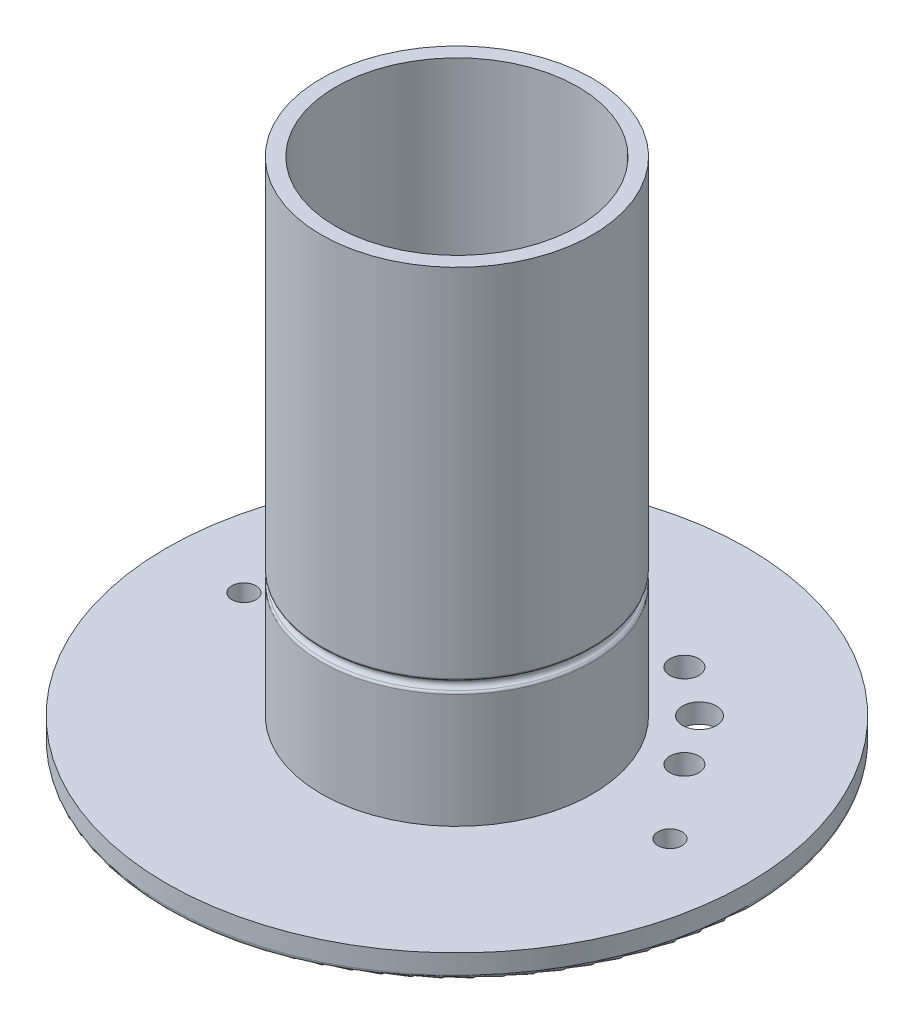
SolidWorks part; units mm, degrees
ref_plane "Front Plane" through (0, 0, 0) normal (0, 0, 1) x (1, 0, 0)
ref_plane "Top Plane" through (0, 0, 0) normal (0, 1, 0) x (1, 0, 0)
ref_plane "Right Plane" through (0, 0, 0) normal (1, 0, 0) x (0, 0, -1)
sketch "Sketch1" plane through (0, 0, 0) normal (0, 1, 0) x (1, 0, 0)
  circle A0 centre (0, 0) radius 60
extrude "Boss-Extrude1" add sketch "Sketch1" along normal blind 5
sketch "Sketch2" plane through (0, 5, 0) normal (0, 1, 0) x (1, 0, 0)
  circle A1 centre (-44, 0) radius 2.5
  circle A2 centre (44, 0) radius 2.5
extrude "Cut-Extrude1" cut sketch "Sketch2" against normal blind 5
sketch "Sketch3" plane through (0, 5, 0) normal (0, 1, 0) x (1, 0, 0)
  circle A0 centre (0, 0) radius 28
extrude "Boss-Extrude2" add sketch "Sketch3" along normal blind 100
sketch "Sketch5" plane through (0, 105, 0) normal (0, 1, 0) x (1, 0, 0)
  circle A0 centre (0, 0) radius 25
extrude "Cut-Extrude3" cut sketch "Sketch5" against normal blind 105
ref_axis "Axis1" through (0, 105, 0) along (0, -1, 0)
sketch "Sketch6" plane through (0, 5, 0) normal (0, 1, 0) x (1, 0, 0)
  line L0 (0, 28) -> (0, 60)
  circle A0 centre (0, 0) radius 28 construction
  circle A1 centre (0, 0) radius 60 construction
ref_plane "Plane1" through (0, 0, 0) normal (1, 0, 0) x (0, 0, -1)
sketch "Sketch7" plane through (0, 0, 0) normal (1, 0, 0) x (0, 0, -1)
  line L2 (28, 5) -> (28, 105) construction
  circle A0 centre (28, 30) radius 1
revolve "Cut-Revolve1" cut sketch "Sketch7" angle 360 about axis through (0, 105, 0) along (0, -1, 0)
fillet "Fillet2" radius 1 1 edges at (0, 0, 60)
fillet "Fillet3" radius 0.5 1 edges at (0, 29, 28)
fillet "Fillet4" radius 0.5 1 edges at (0, 31, -28)
sketch "Sketch9" plane through (0, 0, 0) normal (0, -1, 0) x (1, 0, 0)
  circle A4 centre (-25.0503, -25.0501) radius 3.5
  circle A5 centre (25.0521, -25.0478) radius 3.5
  circle A16 centre (32.192, -14.7876) radius 3
  circle A17 centre (14.7931, -32.1895) radius 3
  circle A19 centre (-14.7905, -32.1907) radius 3
  circle A20 centre (-32.192, -14.7876) radius 3
extrude "Cut-Extrude4" cut sketch "Sketch9" against normal blind 5
sketch "Sketch10" plane through (0, 0, 0) normal (0, -1, 0) x (1, 0, 0)
  circle A0 centre (-25.0503, -25.0501) radius 5
  circle A1 centre (25.0521, -25.0478) radius 5
extrude "Cut-Extrude6" cut sketch "Sketch10" against normal blind 1
sketch "Sketch11" plane through (0, 0, 0) normal (0, -1, 0) x (1, 0, 0)
  circle A0 centre (-32.192, -14.7876) radius 5
  circle A1 centre (-14.7905, -32.1907) radius 5
extrude "Cut-Extrude7" cut sketch "Sketch11" against normal blind 2
